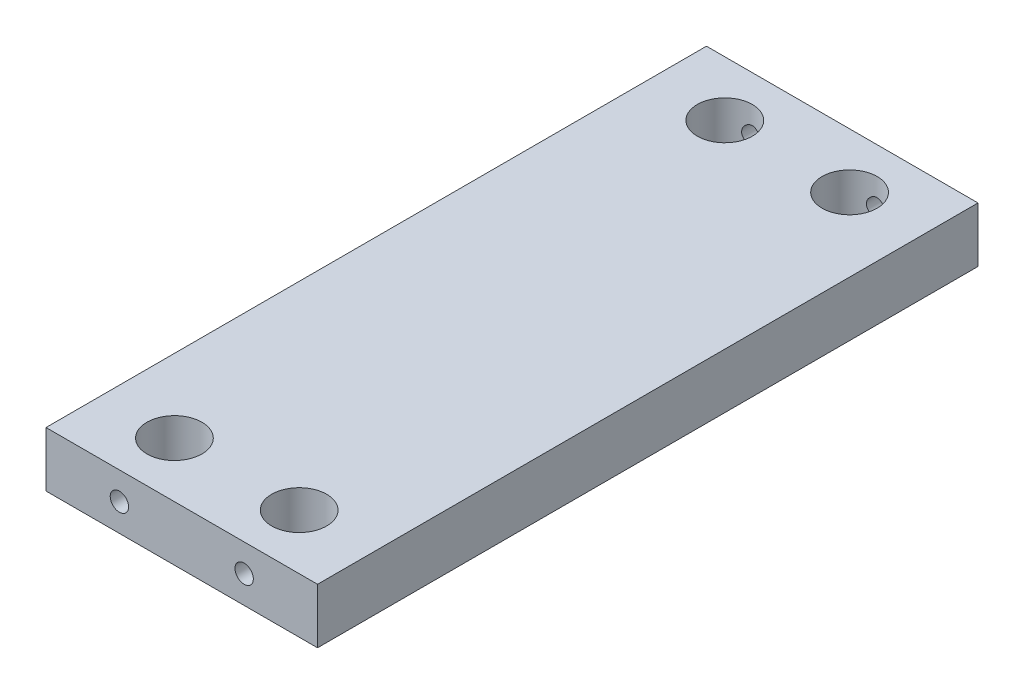
SolidWorks part; units mm, degrees
material "Pine"
ref_plane "Front Plane" through (0, 0, 0) normal (0, 0, 1) x (1, 0, 0)
ref_plane "Top Plane" through (0, 0, 0) normal (0, 1, 0) x (1, 0, 0)
ref_plane "Right Plane" through (0, 0, 0) normal (1, 0, 0) x (0, 0, -1)
sketch "Sketch1" plane through (0, 0, 0) normal (0, 1, 0) x (1, 0, 0)
  line L1 (-46.99, 114.3) -> (46.99, 114.3)
  line L2 (-46.99, 114.3) -> (-46.99, -114.3)
  line L3 (-46.99, -114.3) -> (46.99, -114.3)
  line L4 (46.99, 114.3) -> (46.99, -114.3)
  line L5 (-46.99, 114.3) -> (46.99, -114.3) construction
  line L6 (-46.99, -114.3) -> (46.99, 114.3) construction
  point P0 (0, 0)
  dimension "D1" = 228.6
  dimension "D2" = 93.98
extrude "Boss-Extrude1" add sketch "Sketch1" along normal blind 19.05
hole_wizard "3/4 (0.75) Diameter Hole1" positions "Sketch3" profile "Sketch2" hole size "3/4" standard "Ansi Inch"
sketch "Sketch3" plane through (0, 19.05, 0) normal (0, 1, 0) x (-1, 0, 0)
  line L0 (46.99, -114.3) -> (46.99, 114.3) construction
  line L1 (-46.99, -114.3) -> (46.99, -114.3) construction
  point P0 (21.59, -95.25)
  dimension "D1" = 25.4
  dimension "D2" = 19.05
sketch "Sketch2" plane through (-21.59, 19.05, -95.25) normal (1, 0, 0) x (0, 0, 1)
  line L0 (0, 0) -> (0, 24.7732)
  line L1 (0, 24.7732) -> (9.525, 19.05)
  line L2 (9.525, 19.05) -> (9.525, 0)
  line L5 (9.525, 0) -> (0, 0)
  line L10 (0, 24.7732) -> (-9.525, 19.05) construction
  line L11 (0, -6.35) -> (0, 107.95) construction
  dimension "Hole Dia." = 19.05
  dimension "Hole Depth" = 19.05
  dimension "Drill Angle" = 118
mirror "Mirror1" about plane through (0, 0, 0) normal (0, 0, 1) of "3/4 (0.75) Diameter Hole1"
mirror "Mirror4" about plane through (0, 0, 0) normal (1, 0, 0) of "Mirror1", "3/4 (0.75) Diameter Hole1"
hole_wizard "1/4 (0.25) Diameter Hole1" positions "Sketch5" profile "Sketch4" hole size "1/4" standard "Ansi Inch"
sketch "Sketch5" plane through (0, 0, -114.3) normal (0, 0, -1) x (-1, 0, 0)
  line L0 (-46.99, 19.05) -> (-46.99, 0) construction
  line L1 (-46.99, 0) -> (46.99, 0) construction
  point P0 (-21.59, 9.525)
  dimension "D1" = 25.4
  dimension "D2" = 9.525
sketch "Sketch4" plane through (21.59, 9.525, -114.3) normal (1, 0, 0) x (0, 1, 0)
  line L0 (0, 0) -> (0, 20.9577)
  line L1 (0, 20.9577) -> (3.175, 19.05)
  line L2 (3.175, 19.05) -> (3.175, 0)
  line L5 (3.175, 0) -> (0, 0)
  line L10 (0, 20.9577) -> (-3.175, 19.05) construction
  line L11 (0, -6.35) -> (0, 107.95) construction
  dimension "Hole Dia." = 6.35
  dimension "Hole Depth" = 19.05
  dimension "Drill Angle" = 118
mirror "Mirror5" about plane through (0, 0, 0) normal (0, 0, 1) of "1/4 (0.25) Diameter Hole1"
mirror "Mirror10" about plane through (0, 0, 0) normal (1, 0, 0) of "Mirror5", "1/4 (0.25) Diameter Hole1"
